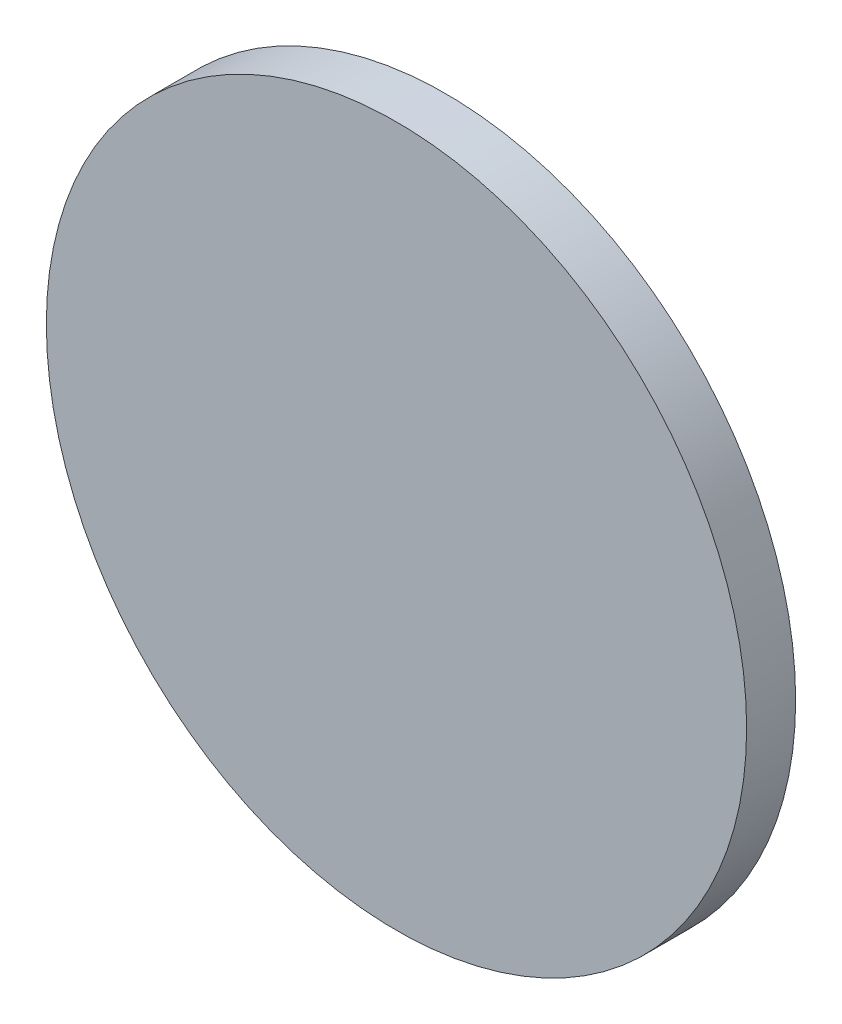
SolidWorks part; units mm, degrees
ref_plane "Plan de face" through (0, 0, 0) normal (0, 0, 1) x (1, 0, 0)
ref_plane "Plan de dessus" through (0, 0, 0) normal (0, 1, 0) x (1, 0, 0)
ref_plane "Plan de droite" through (0, 0, 0) normal (1, 0, 0) x (0, 0, -1)
sketch "Esquisse1" plane through (0, 0, 0) normal (0, 0, 1) x (1, 0, 0)
  circle A0 centre (142, 0) radius 50
  dimension "D1" = 100
extrude "Extrusion1" add sketch "Esquisse1" along normal blind 7
